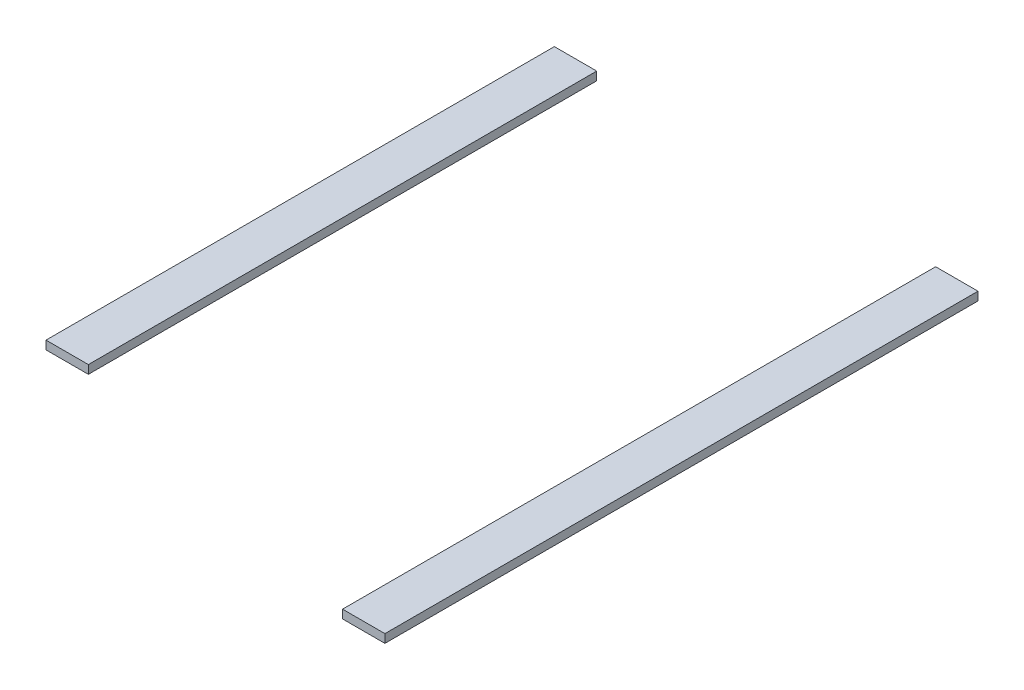
SolidWorks part; units mm, degrees
ref_plane "Front Plane" through (0, 0, 0) normal (0, 0, 1) x (1, 0, 0)
ref_plane "Top Plane" through (0, 0, 0) normal (0, 1, 0) x (1, 0, 0)
ref_plane "Right Plane" through (0, 0, 0) normal (1, 0, 0) x (0, 0, -1)
sketch "Sketch1" plane through (0, 0, 0) normal (0, 1, 0) x (1, 0, 0)
  line L0 (21.25, 15) -> (23.75, 15)
  line L1 (-1.25, 15) -> (1.25, 15)
  line L2 (-1.25, 15) -> (-1.25, -15)
  line L3 (-1.25, -15) -> (1.25, -15)
  line L4 (1.25, 15) -> (1.25, -15)
  line L5 (-1.25, 15) -> (1.25, -15) construction
  line L6 (-1.25, -15) -> (1.25, 15) construction
  line L7 (21.25, 15) -> (21.25, -20)
  line L8 (21.25, -20) -> (23.75, -20)
  line L9 (23.75, 15) -> (23.75, -20)
  point P0 (0, 0)
  point P12 (22.5, 15)
  dimension "D1" = 2.5
  dimension "D2" = 30
  dimension "D3" = 0
  dimension "D4" = 2.5
  dimension "D5" = 25
  dimension "D6" = 35
extrude "Boss-Extrude1" add sketch "Sketch1" along normal blind 0.5
